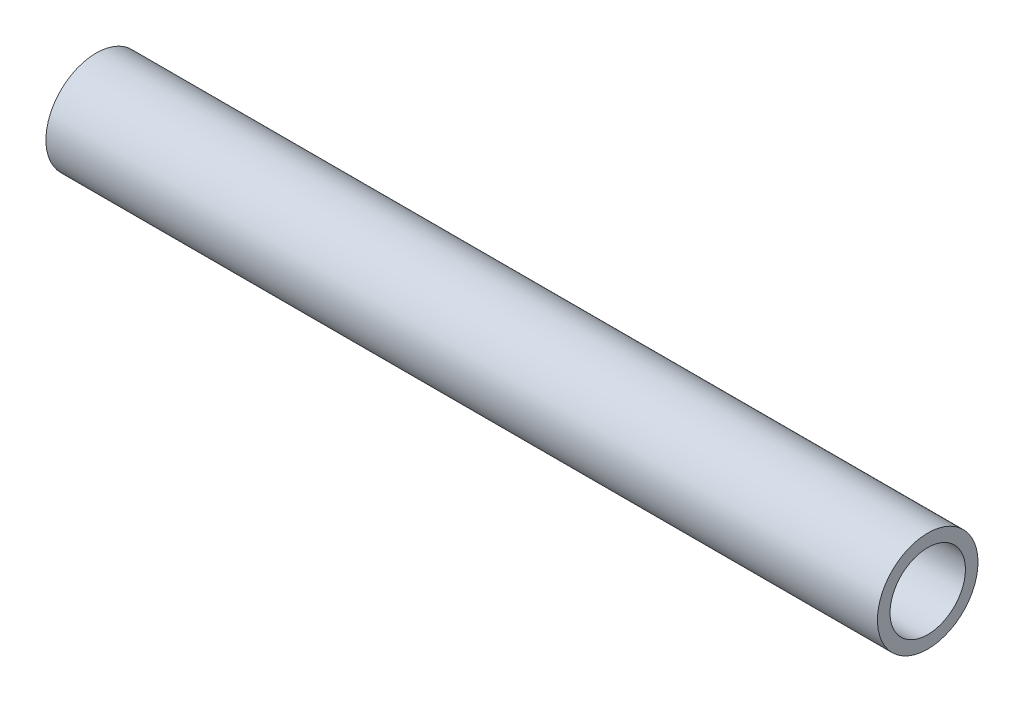
SolidWorks part; units mm, degrees
ref_plane "Front Plane" through (0, 0, 0) normal (0, 0, 1) x (1, 0, 0)
ref_plane "Top Plane" through (0, 0, 0) normal (0, 1, 0) x (1, 0, 0)
ref_plane "Right Plane" through (0, 0, 0) normal (1, 0, 0) x (0, 0, -1)
sketch "Sketch1" plane through (0, 0, 0) normal (1, 0, 0) x (0, 0, -1)
  circle A0 centre (0, 0) radius 9.525
  circle A1 centre (0, 0) radius 12.7
extrude "Boss-Extrude1" add sketch "Sketch1" along normal mid plane 210
